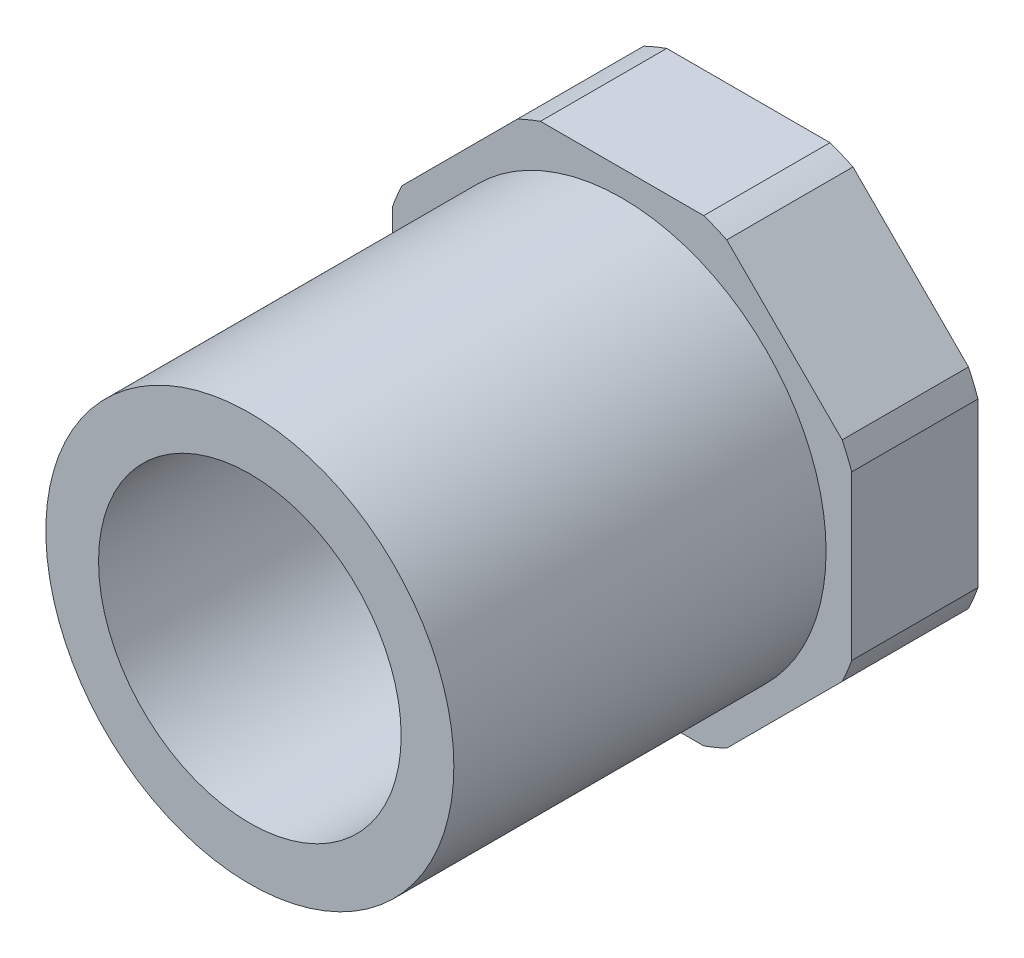
SolidWorks part; units mm, degrees
ref_plane "Front Plane" through (0, 0, 0) normal (0, 0, 1) x (1, 0, 0)
ref_plane "Top Plane" through (0, 0, 0) normal (0, 1, 0) x (1, 0, 0)
ref_plane "Right Plane" through (0, 0, 0) normal (1, 0, 0) x (0, 0, -1)
sketch "Sketch1" plane through (0, 0, 0) normal (1, 0, 0) x (0, 0, -1)
  line L0 (-13.0969, 0) -> (13.0969, 0) construction
  line L1 (6.4611, -10.7188) -> (6.4611, 10.7188) construction
  line L2 (6.4611, -10.7188) -> (-13.0969, -10.7188) construction
  line L3 (-13.0969, -10.7188) -> (-13.0969, -7.9502) construction
  line L4 (-13.0969, -7.9502) -> (4.8736, -7.9502) construction
  line L5 (6.4611, 10.7188) -> (-13.0969, 10.7188) construction
  line L6 (-13.0969, 10.7188) -> (-13.0969, 7.9502) construction
  line L7 (-13.0969, 7.9502) -> (4.8736, 7.9502) construction
  arc A3 (4.8736, -7.9502) -> (4.8736, 7.9502) centre (-14.2399, 0) ccw construction
  point P4 (0, 0)
  point P8 (-13.0969, 0)
  point P9 (6.4611, 0)
  dimension "Wall Thickness" = 2.7686
  dimension "D1" = 1.5875
  dimension "ID" = 15.9004
  dimension "Length" = 26.1937
  dimension "Socket Length" = 19.558
  dimension "OD" = 21.4376
sketch "Sketch2" plane through (0, 0, 0) normal (0, 0, 1) x (1, 0, 0)
  line L0 (0, 12.065) -> (0, -12.065) construction
  circle A1 centre (0, 0) radius 10.7188 construction
  point P5 (0, 0)
  point P12 (0, -10.7188)
  point P14 (10.7188, 0)
  point P15 (-10.7188, 0)
  point P16 (0, 10.7188)
  dimension "D1" = 21.4376
  dimension "Drive Size" = 24.13
sketch "Sketch3" plane through (0, 0, 0) normal (1, 0, 0) x (0, 0, -1)
  line L0 (6.4611, 0) -> (13.0969, 0)
  line L1 (13.0969, 0) -> (13.0969, -10.7188)
  line L2 (13.0969, -10.7188) -> (-13.0969, -10.7188)
  line L3 (-13.0969, -10.7188) -> (-13.0969, -7.9502)
  line L4 (-13.0969, -7.9502) -> (4.8736, -7.9502)
  arc A4 (4.8736, -7.9502) -> (4.8736, 7.9502) centre (-14.2399, 0) ccw construction
  arc A5 (4.8736, -7.9502) -> (6.4611, 0) centre (-14.2399, 0) ccw
revolve "Revolve1" add sketch "Sketch3" angle 360 about L0
sketch "Sketch4" plane through (0, 0, -13.0969) normal (0, 0, -1) x (-1, 0, 0)
  line L0 (-4.9975, 12.065) -> (4.9975, -12.065) construction
  line L3 (4.9975, 12.065) -> (-4.9975, 12.065)
  line L4 (-4.9975, 12.065) -> (-12.065, 4.9975)
  line L20 (-12.065, 4.9975) -> (-12.065, -4.9975)
  line L21 (-12.065, -4.9975) -> (-4.9975, -12.065)
  line L22 (-4.9975, -12.065) -> (4.9975, -12.065)
  line L23 (4.9975, -12.065) -> (12.065, -4.9975)
  line L24 (12.065, -4.9975) -> (12.065, 4.9975)
  line L25 (12.065, 4.9975) -> (4.9975, 12.065)
  circle A2 centre (0, 0) radius 12.065 construction
  circle A3 centre (0, 0) radius 10.7188 construction
  circle A4 centre (0, 0) radius 10.7188
extrude "Boss-Extrude1" add sketch "Sketch4" against normal up to vertex (6.6357 mm away) up to point (0, 10.7188, -6.4611)
ref_plane "Plane1" through (0, 0, 0) normal (0.9239, -0.3827, 0) x (0, 0, -1)
sketch "Sketch5" plane through (0, 0, 0) normal (0.9239, -0.3827, 0) x (0, 0, -1)
  line L1 (6.4611, 13.0591) -> (13.0969, 13.0591)
  line L2 (6.4611, 13.0591) -> (6.4611, 12.8051)
  line L3 (6.4611, 12.8051) -> (13.0969, 12.8051)
  line L4 (13.0969, 13.0591) -> (13.0969, 12.8051)
  dimension "D1" = 0.254
revolve "Cut-Revolve1" cut sketch "Sketch5" angle 360 about axis through (0, 0, 13.0969) along (0, 0, 1)
equation "\"D1\"= \"Drive Length@Sketch1\""
equation "\"D1@Sketch2\"= \"OD@Sketch1\""
